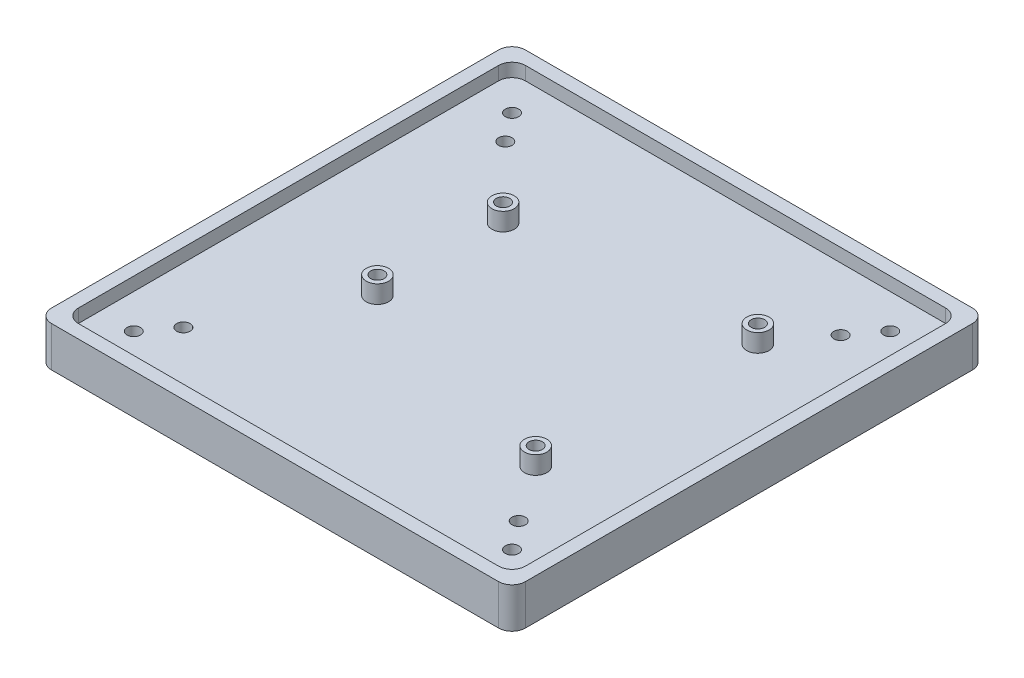
SolidWorks part; units mm, degrees
ref_plane "Front Plane" through (0, 0, 0) normal (0, 0, 1) x (1, 0, 0)
ref_plane "Top Plane" through (0, 0, 0) normal (0, 1, 0) x (1, 0, 0)
ref_plane "Right Plane" through (0, 0, 0) normal (1, 0, 0) x (0, 0, -1)
sketch "Sketch1" plane through (0, 0, 0) normal (0, 1, 0) x (1, 0, 0)
  line L0 (0, 51) -> (0, -49) construction
  line L1 (-72.9844, 51) -> (72.9844, 51)
  line L2 (-72.9844, 51) -> (-72.9844, -49)
  line L3 (-72.9844, -49) -> (72.9844, -49)
  line L4 (72.9844, 51) -> (72.9844, -49)
  line L5 (72.9844, 1) -> (-72.9844, 1) construction
  line L10 (-3.0156, 29) -> (72.9844, 29) construction
  line L11 (72.9844, 29) -> (72.9844, -25.5) construction
  line L12 (72.9844, -25.5) -> (-3.0156, -25.5) construction
  line L13 (-3.0156, -25.5) -> (-3.0156, 29) construction
  circle A0 centre (52.9844, 26) radius 1.5
  circle A1 centre (0.9844, 21) radius 1.5
  circle A2 centre (0.9844, -7.1) radius 1.5
  circle A3 centre (51.7844, -22.5) radius 1.5
  circle A4 centre (-66.5, 14.15) radius 1.5
  circle A5 centre (-35.9, 14.15) radius 1.5
  circle A6 centre (-66.5, -12.15) radius 1.5
  circle A7 centre (-36.1, -12.15) radius 1.5
  circle A22 centre (-65.4844, 38.5) radius 1.5
  circle A23 centre (-65.4844, -36.5) radius 1.5
  point P34 (-27.2424, -34.4608)
  point P40 (-15.3656, 1)
  dimension "D4" = 3
  dimension "D5" = 26.3
  dimension "D6" = 30.6
  dimension "D7" = 13.15
  dimension "D8" = 52
  dimension "D9" = 5
  dimension "D10" = 28.1
  dimension "D11" = 30
  dimension "D12" = 100
  dimension "D24" = 3
  dimension "D25" = 3
  dimension "D27" = 20
  dimension "D30" = 3
  dimension "D32" = 3
  dimension "D40" = 7.5
  dimension "D41" = 48.5
  dimension "D42" = 30.4
  dimension "D1" = 0
  dimension "D13" = 50.8
  dimension "D34" = 0
extrude "Boss-Extrude1" add sketch "Sketch1" along normal blind 6
sketch "Sketch4" plane through (0, 6, 0) normal (0, 1, 0) x (1, 0, 0)
  circle A0 centre (51.7844, -22.5) radius 2.5
  circle A1 centre (51.7844, -22.5) radius 1.5
  circle A2 centre (52.9844, 26) radius 1.5
  circle A3 centre (52.9844, 26) radius 2.5
  circle A4 centre (0.9844, -7.1) radius 1.5
  circle A5 centre (0.9844, -7.1) radius 2.5
  circle A6 centre (0.9844, 21) radius 1.5
  circle A7 centre (0.9844, 21) radius 2.5
  circle A8 centre (-35.9, 14.15) radius 1.5
  circle A9 centre (-35.9, 14.15) radius 2.5
  circle A10 centre (-36.1, -12.15) radius 1.5
  circle A11 centre (-36.1, -12.15) radius 2.5
  circle A12 centre (-66.5, -12.15) radius 1.5
  circle A13 centre (-66.5, -12.15) radius 2.5
  circle A14 centre (-66.5, 14.15) radius 1.5
  circle A15 centre (-66.5, 14.15) radius 2.5
  dimension "D1" = 3
  dimension "D2" = 3
  dimension "D3" = 3
  dimension "D4" = 3
  dimension "D5" = 3
  dimension "D6" = 3
  dimension "D7" = 3
  dimension "D8" = 3
  dimension "D9" = 1
  dimension "D10" = 1
  dimension "D11" = 1
  dimension "D12" = 1
  dimension "D13" = 1
  dimension "D14" = 1
  dimension "D15" = 1
  dimension "D16" = 1
extrude "Boss-Extrude4" add sketch "Sketch4" along normal blind 4
sketch "Sketch5" plane through (0, 6, 0) normal (0, 1, 0) x (1, 0, 0)
  line L0 (-72.9844, 51) -> (-72.9844, -49) construction
  line L1 (-72.9844, 61.9053) -> (-27.0144, 61.9053)
  line L2 (-72.9844, 61.9053) -> (-72.9844, -72.908)
  line L3 (-72.9844, -72.908) -> (-27.0144, -72.908)
  line L4 (-27.0144, 61.9053) -> (-27.0144, -72.908)
  dimension "D1" = 45.97
extrude "Cut-Extrude3" cut sketch "Sketch5" against normal blind 10
sketch "Sketch7" plane through (0, 6, 0) normal (0, 1, 0) x (1, 0, 0)
  line L4 (-27.0144, 51) -> (-27.0144, -49)
  line L5 (-27.0144, -49) -> (72.9844, -49)
  line L6 (72.9844, -49) -> (72.9844, 51)
  line L7 (72.9844, 51) -> (-27.0144, 51)
  line L8 (-30.0144, 54) -> (-30.0144, -52)
  line L9 (-30.0144, -52) -> (75.9844, -52)
  line L10 (75.9844, -52) -> (75.9844, 54)
  line L11 (75.9844, 54) -> (-30.0144, 54)
  line L12 (-30.0144, 54) -> (-30.0144, -52)
  line L13 (-30.0144, -52) -> (75.9844, -52)
  line L14 (75.9844, -52) -> (75.9844, 54)
  line L15 (75.9844, 54) -> (-30.0144, 54)
  dimension "D1" = 3
extrude "Boss-Extrude5" add sketch "Sketch7" along normal blind 3 and the other way blind 6
fillet "Fillet1" radius 3 8 edges at (-30.0144, 4.5, -54) (75.9844, 4.5, -54) (75.9844, 4.5, 52) (-30.0144, 4.5, 52) (-27.0144, 7.5, 49) (-27.0144, 7.5, -51) (72.9844, 7.5, 49) (72.9844, 7.5, -51)
sketch "Sketch8" plane through (0, 6, 0) normal (0, 1, 0) x (1, 0, 0)
  line L0 (-24.0144, -49) -> (69.9844, -49) construction
  line L3 (72.9844, -46) -> (72.9844, 48) construction
  line L4 (-27.0144, -46) -> (-27.0144, 48) construction
  circle A0 centre (65.2844, -41.3) radius 1.5
  circle A1 centre (65.2844, 43.3) radius 1.5
  circle A2 centre (-19.3144, -41.3) radius 1.5
  circle A3 centre (-19.3144, 43.3) radius 1.5
  dimension "D1" = 84.6
  dimension "D4" = 3
  dimension "D5" = 3
  dimension "D6" = 3
  dimension "D7" = 3
  dimension "D2" = 7.7
  dimension "D3" = 7.7
  dimension "D8" = 84.6
  dimension "D9" = 7.7
extrude "Cut-Extrude4" cut sketch "Sketch8" against normal blind 10
sketch "Sketch9" plane through (0, 6, 0) normal (0, 1, 0) x (1, 0, 0)
  circle A0 centre (-14.5144, -35) radius 1.5
  circle A1 centre (-19.3144, -41.3) radius 1.5 construction
  circle A2 centre (-14.5144, 37) radius 1.5
  circle A3 centre (60.4844, -35) radius 1.5
  circle A4 centre (60.4844, 37) radius 1.5
  circle A5 centre (-19.3144, 43.3) radius 1.5 construction
  circle A6 centre (65.2844, -41.3) radius 1.5 construction
  circle A7 centre (65.2844, 43.3) radius 1.5 construction
  dimension "D1" = 6.3
  dimension "D5" = 6.3
  dimension "D6" = 4.8
  dimension "D7" = 4.8
  dimension "D8" = 6.3
  dimension "D9" = 3
  dimension "D2" = 4.8
  dimension "D3" = 4.8
  dimension "D4" = 6.3
extrude "Cut-Extrude5" cut sketch "Sketch9" against normal through all
sketch "Sketch10" plane through (0, 0, 0) normal (0, -1, 0) x (-1, 0, 0)
  circle A0 centre (19.3144, 43.3) radius 3
  circle A1 centre (19.3144, -41.3) radius 3
  circle A2 centre (-65.2844, -41.3) radius 3
  circle A3 centre (-65.2844, 43.3) radius 3
  dimension "D1" = 6
  dimension "D2" = 6
  dimension "D3" = 6
  dimension "D4" = 6
extrude "Cut-Extrude6" cut sketch "Sketch10" against normal blind 3
